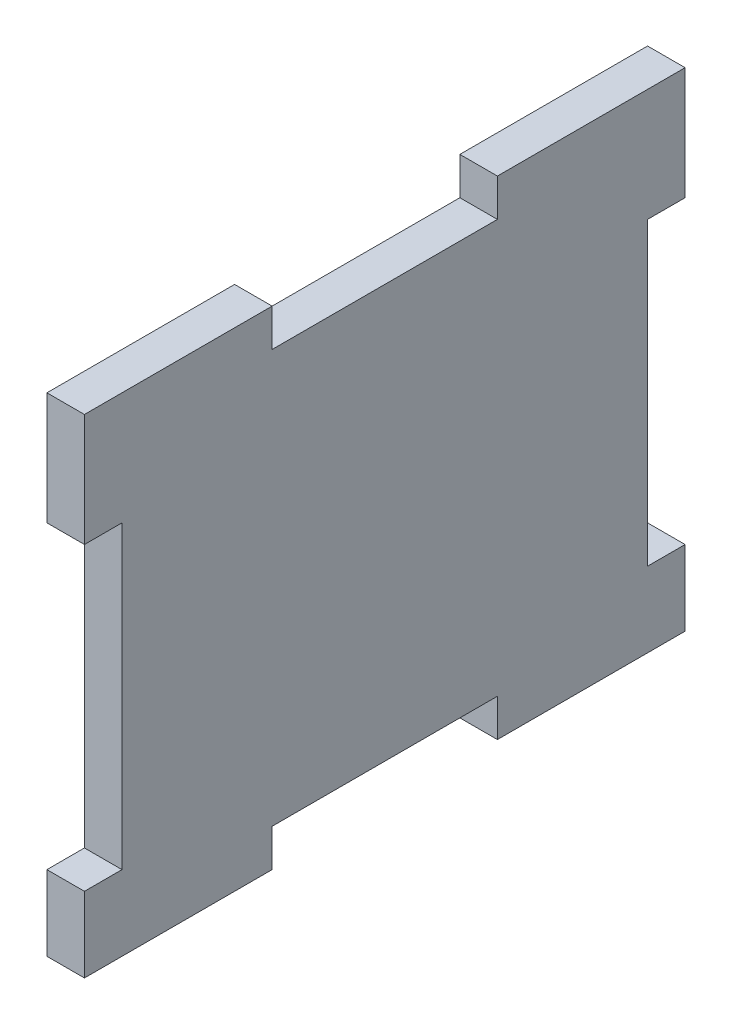
SolidWorks part; units mm, degrees
ref_plane "Front Plane" through (0, 0, 0) normal (0, 0, 1) x (1, 0, 0)
ref_plane "Top Plane" through (0, 0, 0) normal (0, 1, 0) x (1, 0, 0)
ref_plane "Right Plane" through (0, 0, 0) normal (1, 0, 0) x (0, 0, -1)
sketch "Sketch1" plane through (0, 0, 0) normal (1, 0, 0) x (0, 0, -1)
  line L1 (-50.8, -41.275) -> (50.8, -41.275)
  line L2 (-50.8, -41.275) -> (-50.8, 41.275)
  line L3 (-50.8, 41.275) -> (50.8, 41.275)
  line L4 (50.8, -41.275) -> (50.8, 41.275)
  line L5 (-50.8, -41.275) -> (50.8, 41.275) construction
  line L6 (-50.8, 41.275) -> (50.8, -41.275) construction
  line L7 (-19.05, -41.275) -> (19.05, -41.275)
  line L8 (-19.05, -41.275) -> (-19.05, -34.925)
  line L9 (-19.05, -34.925) -> (19.05, -34.925)
  line L10 (19.05, -41.275) -> (19.05, -34.925)
  line L11 (-50.8, -28.575) -> (-44.45, -28.575)
  line L12 (-50.8, -28.575) -> (-50.8, 22.225)
  line L13 (-50.8, 22.225) -> (-44.45, 22.225)
  line L14 (-44.45, -28.575) -> (-44.45, 22.225)
  line L15 (50.8, -28.575) -> (44.45, -28.575)
  line L16 (50.8, -28.575) -> (50.8, 22.225)
  line L17 (50.8, 22.225) -> (44.45, 22.225)
  line L18 (44.45, -28.575) -> (44.45, 22.225)
  line L19 (-19.05, 41.275) -> (19.05, 41.275)
  line L20 (-19.05, 41.275) -> (-19.05, 34.925)
  line L21 (-19.05, 34.925) -> (19.05, 34.925)
  line L22 (19.05, 41.275) -> (19.05, 34.925)
  point P0 (0, 0)
  dimension "D1" = 101.6
  dimension "D2" = 82.55
  dimension "D3" = 6.35
  dimension "D4" = 31.75
  dimension "D5" = 31.75
  dimension "D6" = 6.35
  dimension "D7" = 6.35
  dimension "D8" = 12.7
  dimension "D9" = 19.05
  dimension "D10" = 6.35
extrude "Boss-Extrude1" add sketch "Sketch1" along normal blind 6.35 contours L10 L1 L4 L3 L2 L8 L9
